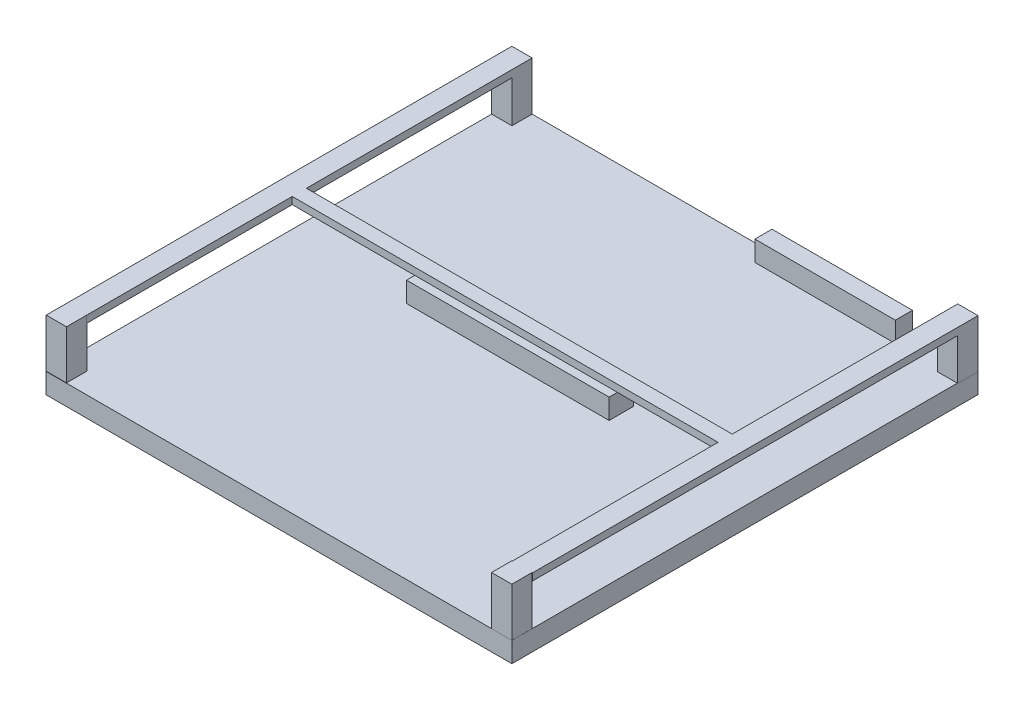
SolidWorks part; units mm, degrees
ref_plane "Front Plane" through (0, 0, 0) normal (0, 0, 1) x (1, 0, 0)
ref_plane "Top Plane" through (0, 0, 0) normal (0, 1, 0) x (1, 0, 0)
ref_plane "Right Plane" through (0, 0, 0) normal (1, 0, 0) x (0, 0, -1)
sketch "Sketch1" plane through (0, 0, 0) normal (0, 1, 0) x (1, 0, 0)
  line L1 (-57.5, -57.5) -> (57.5, -57.5)
  line L2 (-57.5, -57.5) -> (-57.5, 57.5)
  line L3 (-57.5, 57.5) -> (57.5, 57.5)
  line L4 (57.5, -57.5) -> (57.5, 57.5)
  line L5 (-57.5, -57.5) -> (57.5, 57.5) construction
  line L6 (-57.5, 57.5) -> (57.5, -57.5) construction
  point P0 (0, 0)
  dimension "D1" = 115
  dimension "D2" = 115
extrude "Boss-Extrude3" add sketch "Sketch1" along normal blind 5 contours L3 L4 L1 L2
sketch "Sketch5" plane through (0, 5, 0) normal (0, 1, 0) x (1, 0, 0)
  line L0 (-57.5, -57.5) -> (57.5, -57.5) construction
  line L1 (-27.5, 7.5) -> (22.5, 7.5)
  line L2 (-27.5, 7.5) -> (-27.5, 1.5)
  line L3 (-27.5, 1.5) -> (22.5, 1.5)
  line L4 (22.5, 7.5) -> (22.5, 1.5)
  line L5 (-57.5, -57.5) -> (-57.5, 57.5) construction
  line L6 (-57.5, 57.5) -> (57.5, 57.5) construction
  line L7 (6.7052, 57.5) -> (41.3834, 57.5)
  line L8 (6.7052, 57.5) -> (6.7052, 53.2745)
  line L9 (6.7052, 53.2745) -> (41.3834, 53.2745)
  line L10 (41.3834, 57.5) -> (41.3834, 53.2745)
  dimension "D1" = 65
  dimension "D2" = 50
  dimension "D3" = 6
  dimension "D4" = 30
extrude "Boss-Extrude4" add sketch "Sketch5" along normal blind 5
sketch "Sketch6" plane through (0, 5, 0) normal (0, 1, 0) x (1, 0, 0)
  line L0 (-57.5032, -52.4364) -> (-52.5032, -52.4364)
  line L1 (-57.5, 57.5) -> (-52.5, 57.5)
  line L2 (-57.5, 57.5) -> (-57.5, 52.5)
  line L3 (-57.5, 52.5) -> (-52.5, 52.5)
  line L4 (-52.5, 57.5) -> (-52.5, 52.5)
  line L5 (-57.5032, -52.4364) -> (-57.5032, -57.4364)
  line L6 (-57.5032, -57.4364) -> (-52.5032, -57.4364)
  line L7 (-52.5032, -52.4364) -> (-52.5032, -57.4364)
  line L8 (52.608, 57.4508) -> (57.608, 57.4508)
  line L9 (52.608, 57.4508) -> (52.608, 52.4508)
  line L10 (52.608, 52.4508) -> (57.608, 52.4508)
  line L11 (57.608, 57.4508) -> (57.608, 52.4508)
  line L12 (52.4888, -52.5032) -> (57.4888, -52.5032)
  line L13 (52.4888, -52.5032) -> (52.4888, -57.5032)
  line L14 (52.4888, -57.5032) -> (57.4888, -57.5032)
  line L15 (57.4888, -52.5032) -> (57.4888, -57.5032)
  dimension "D1" = 5
  dimension "D2" = 5
extrude "Boss-Extrude5" add sketch "Sketch6" along normal blind 12
sketch "Sketch8" plane through (0, 0, -52.5) normal (0, 0, 1) x (1, 0, 0)
  line L0 (-52.5, 17) -> (-52.5, 5) construction
  line L1 (-57.5, 17) -> (-52.5, 17)
  line L2 (-57.5, 17) -> (-57.5, 15.25)
  line L3 (-57.5, 15.25) -> (-52.5, 15.25)
  line L4 (-52.5, 17) -> (-52.5, 15.25)
  dimension "D1" = 1.75
extrude "Boss-Extrude7" add sketch "Sketch8" along normal blind 105
sketch "Sketch9" plane through (0, 0, -52.4508) normal (0, 0, 1) x (1, 0, 0)
  line L0 (57.608, 17) -> (57.608, 5) construction
  line L1 (52.608, 17) -> (57.608, 17)
  line L2 (52.608, 17) -> (52.608, 15.25)
  line L3 (52.608, 15.25) -> (57.608, 15.25)
  line L4 (57.608, 17) -> (57.608, 15.25)
  dimension "D1" = 1.75
extrude "Boss-Extrude8" add sketch "Sketch9" along normal blind 105
ref_plane "Plane1" through (-52.5, 17, -57.5) normal (0, -1, 0) x (-1, 0, 0)
sketch "Sketch11" plane through (-52.5, 0, 0) normal (1, 0, 0) x (0, 0, -1)
  line L0 (-52.5, 17) -> (57.5, 17) construction
  line L1 (-1.7164, 17) -> (1.7836, 17)
  line L2 (-1.7164, 17) -> (-1.7164, 15.25)
  line L3 (-1.7164, 15.25) -> (1.7836, 15.25)
  line L4 (1.7836, 17) -> (1.7836, 15.25)
  line L5 (-52.5, 15.25) -> (52.5, 15.25) construction
  line L6 (-57.4364, 17) -> (-57.4364, 5) construction
  dimension "D1" = 3.5
  dimension "D2" = 55.72
extrude "Boss-Extrude10" add sketch "Sketch11" along normal blind 108 contours L4 L3 L2 L1
